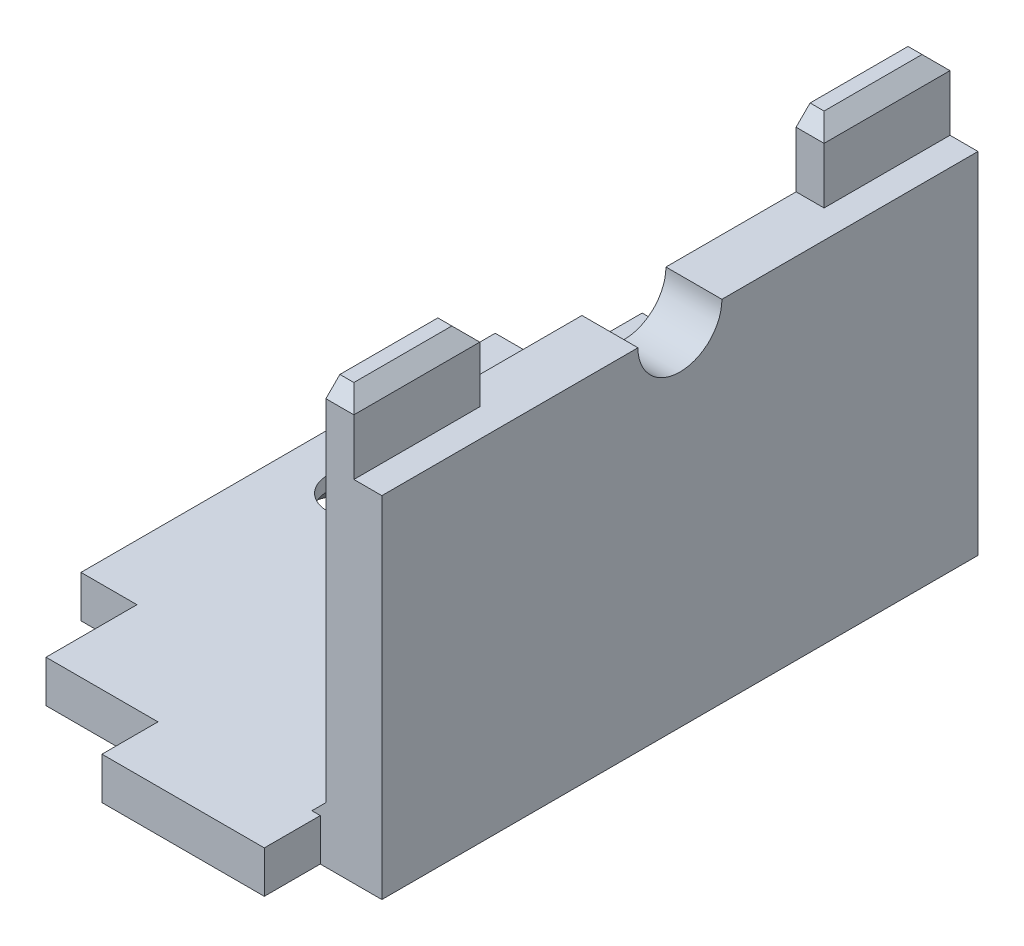
SolidWorks part; units mm, degrees
ref_plane "Front Plane" through (0, 0, 0) normal (0, 0, 1) x (1, 0, 0)
ref_plane "Top Plane" through (0, 0, 0) normal (0, 1, 0) x (1, 0, 0)
ref_plane "Right Plane" through (0, 0, 0) normal (1, 0, 0) x (0, 0, -1)
sketch "Sketch1" plane through (0, 0, 0) normal (0, 1, 0) x (1, 0, 0)
  line L1 (0, 0) -> (12, 0)
  line L2 (0, 0) -> (0, 21.3)
  line L3 (0, 21.3) -> (12, 21.3)
  line L4 (12, 0) -> (12, 21.3)
  dimension "D1" = 12
  dimension "D2" = 21.3
extrude "Boss-Extrude1" add sketch "Sketch1" along normal blind 1.5
sketch "Sketch2" plane through (0, 1.5, 0) normal (0, 1, 0) x (1, 0, 0)
  line L0 (0, 0) -> (12, 0) construction
  line L1 (12, 21.3) -> (10, 21.3)
  line L2 (12, 21.3) -> (12, 0)
  line L3 (12, 0) -> (10, 0)
  line L4 (10, 21.3) -> (10, 0)
  dimension "D1" = 2
extrude "Boss-Extrude2" add sketch "Sketch2" along normal blind 11
sketch "Sketch3" plane through (0, 1.5, 0) normal (0, 1, 0) x (1, 0, 0)
  line L0 (0, 10.65) -> (10, 10.65) construction
  line L1 (0, 21.3) -> (0, 0) construction
  line L2 (10, 21.3) -> (10, 0) construction
  line L4 (0, 18.05) -> (-2, 18.05)
  line L5 (0, 18.05) -> (0, 3.25)
  line L6 (0, 3.25) -> (-2, 3.25)
  line L7 (-2, 18.05) -> (-2, 3.25)
  dimension "D1" = 14.8
  dimension "D2" = 2
extrude "Boss-Extrude3" add sketch "Sketch3" against normal up to surface (1.5 mm away) up to face at (6, 0, -10.65)
sketch "Sketch4" plane through (10, 0, 0) normal (-1, 0, 0) x (0, 0, 1)
  line L0 (-21.3, 12.5) -> (0, 12.5) construction
  circle A0 centre (-10.65, 12.5) radius 1.5
  dimension "D1" = 3
extrude "Cut-Extrude1" cut sketch "Sketch4" against normal up to surface (2 mm away) up to face at (12, 6.25, -10.65)
chamfer "Chamfer1" distance 0.5 angle 45 1 edges
sketch "Sketch5" plane through (0, 1.5, 0) normal (0, 1, 0) x (1, 0, 0)
  circle A0 centre (0.5, 10.65) radius 1.1
  dimension "D1" = 2.2
extrude "Cut-Extrude2" cut sketch "Sketch5" against normal up to next
chamfer "Chamfer2" distance 1 angle 45 1 edges at (0.5, 0, -11.75)
sketch "Sketch6" plane through (0, 12.5, 0) normal (0, 1, 0) x (1, 0, 0)
  line L0 (10, 9.15) -> (10, 0) construction
  line L1 (10, 4.5) -> (11, 4.5)
  line L2 (10, 4.5) -> (10, 0)
  line L3 (10, 0) -> (11, 0)
  line L4 (11, 4.5) -> (11, 0)
  line L5 (10, 0) -> (12, 0) construction
  line L6 (10, 21.3) -> (10, 12.15) construction
  line L7 (10, 16.8) -> (11, 16.8)
  line L8 (10, 16.8) -> (10, 21.3)
  line L9 (10, 21.3) -> (11, 21.3)
  line L10 (11, 16.8) -> (11, 21.3)
  line L11 (12, 21.3) -> (10, 21.3) construction
  dimension "D1" = 4.5
extrude "Boss-Extrude4" add sketch "Sketch6" along normal blind 2.5
chamfer "Chamfer3" distance 0.5 angle 45 6 edges at (10.5, 15, -21.3) (11, 15, -19.05) (10.5, 15, -16.8) (10.5, 15, -4.5) (11, 15, -2.25) (10.5, 15, 0)
sketch "Sketch7" plane through (0, 0, 0) normal (0, 0, 1) x (1, 0, 0)
  line L0 (0, 0) -> (12, 0) construction
  line L1 (9.8, 0) -> (4, 0)
  line L2 (9.8, 0) -> (9.8, 1.5)
  line L3 (9.8, 1.5) -> (4, 1.5)
  line L4 (4, 0) -> (4, 1.5)
  line L5 (0, 1.5) -> (9.5, 1.5) construction
  line L6 (12, 12.5) -> (12, 0) construction
  dimension "D1" = 2.2
  dimension "D2" = 5.8
extrude "Boss-Extrude5" add sketch "Sketch7" along normal blind 2
